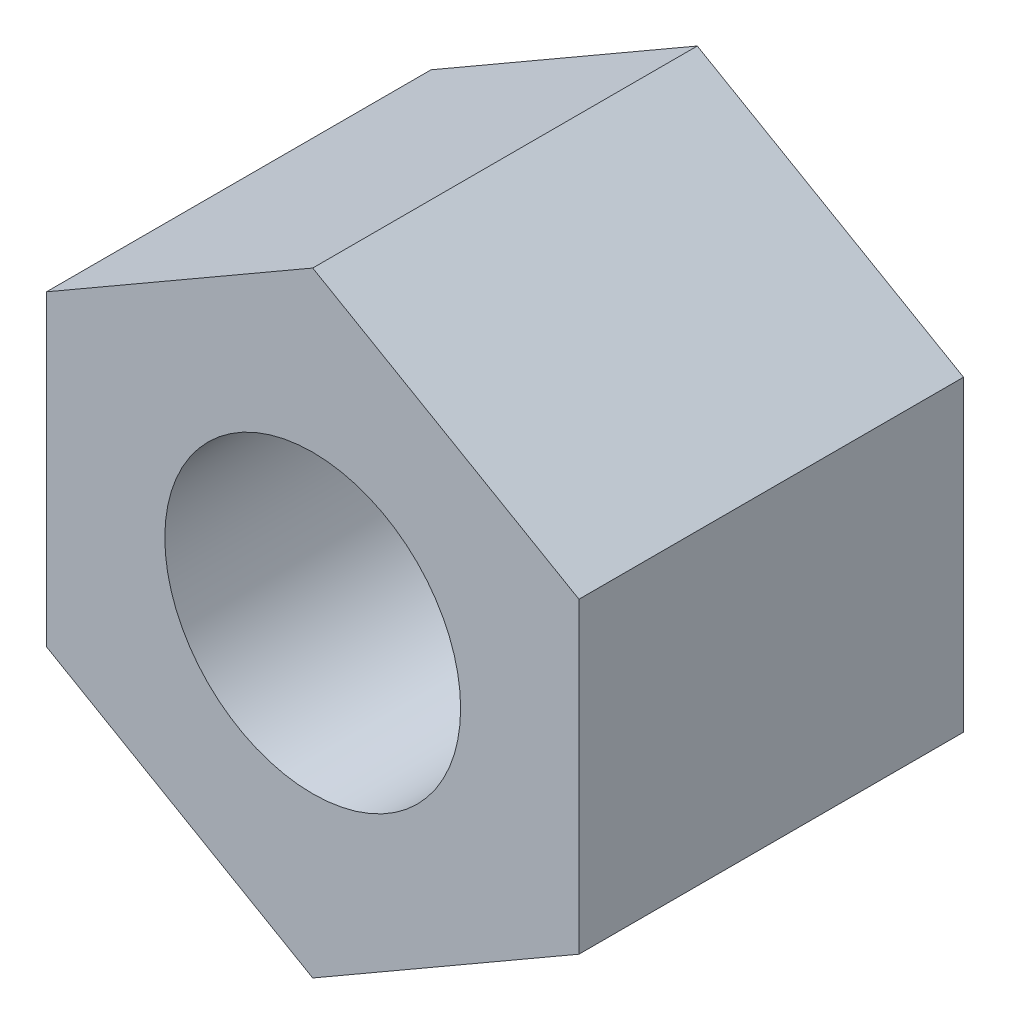
SolidWorks part; units mm, degrees
material "AISI Type A2 Tool Steel"
ref_plane "Front" through (0, 0, 0) normal (0, 0, 1) x (1, 0, 0)
ref_plane "Top" through (0, 0, 0) normal (0, 1, 0) x (1, 0, 0)
ref_plane "Right" through (0, 0, 0) normal (1, 0, 0) x (0, 0, -1)
sketch "Sketch1" plane through (0, 0, 0) normal (0, 0, 1) x (1, 0, 0)
  line L1 (0, 3.1177) -> (-2.7, 1.5588)
  line L2 (-2.7, 1.5588) -> (-2.7, -1.5588)
  line L3 (-2.7, -1.5588) -> (0, -3.1177)
  line L4 (0, -3.1177) -> (2.7, -1.5588)
  line L5 (2.7, -1.5588) -> (2.7, 1.5588)
  line L6 (2.7, 1.5588) -> (0, 3.1177)
  circle A0 centre (0, 0) radius 2.7 construction
  circle A1 centre (0, 0) radius 1.5
  dimension "D1" = 3
  dimension "D2" = 5.4
extrude "Boss-Extrude1" add sketch "Sketch1" along normal blind 3.9
